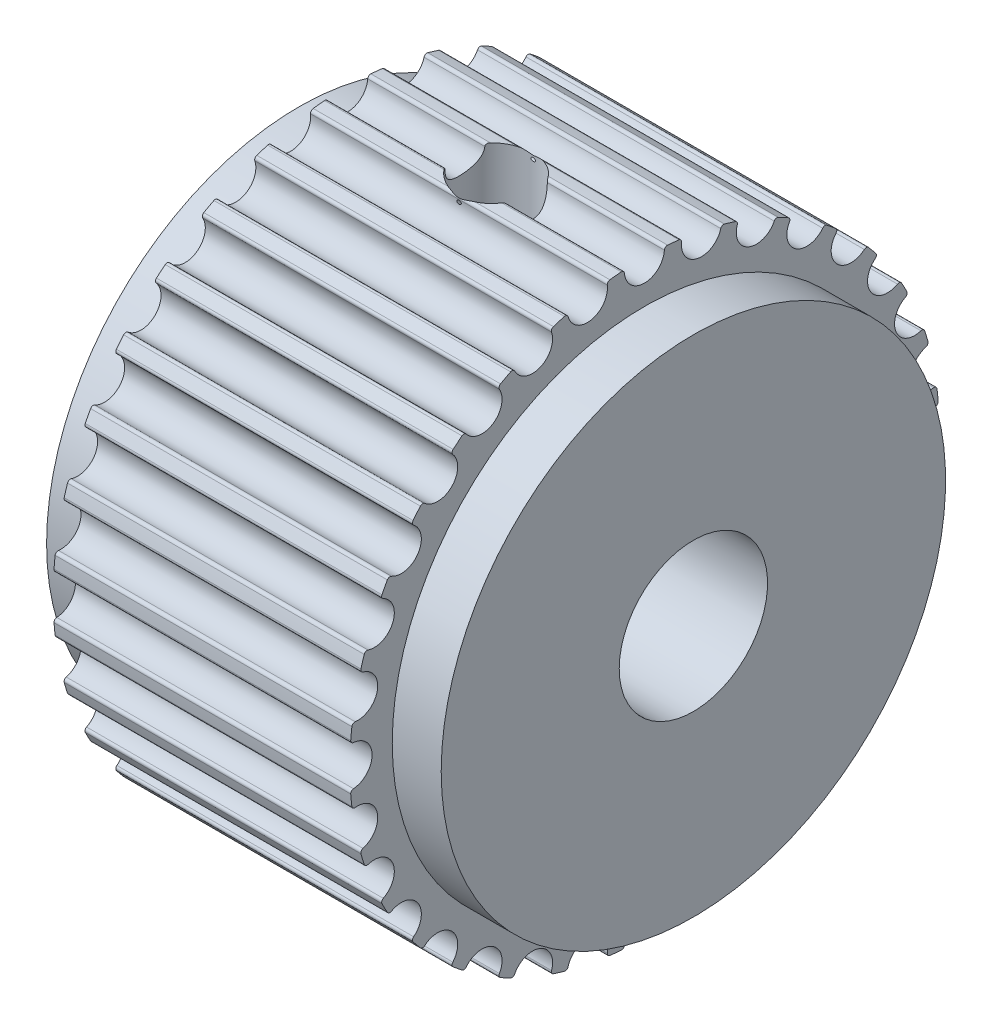
SolidWorks part; units mm, degrees
ref_plane "Front Plane" through (0, 0, 0) normal (0, 0, 1) x (1, 0, 0)
ref_plane "Top Plane" through (0, 0, 0) normal (0, 1, 0) x (1, 0, 0)
ref_plane "Right Plane" through (0, 0, 0) normal (1, 0, 0) x (0, 0, -1)
sketch "Sketch1" plane through (0, 0, 0) normal (0, 0, 1) x (1, 0, 0)
  line L0 (1.65, 10.185) -> (11.65, 10.185) construction
  line L1 (1.65, 9.93) -> (11.65, 9.93)
  line L2 (0, 8.5) -> (0, 2.5)
  line L4 (13.3, 8.5) -> (13.3, 2.5)
  line L5 (0, 2.5) -> (13.3, 2.5)
  line L6 (0, 0) -> (13.3, 0) construction
  line L8 (1.65, 8.5) -> (0, 8.5)
  line L9 (11.65, 8.5) -> (11.65, 9.93)
  line L10 (13.3, 8.5) -> (11.65, 8.5)
  line L13 (1.65, 8.5) -> (1.65, 9.93)
  dimension "D2" = 1.65
  dimension "D1" = 1.65
  dimension "O.D." = 19.86
  dimension "W" = 13.3
  dimension "E" = 17
  dimension "P.D." = 20.37
  dimension "A" = 10
  dimension "P" = 5
revolve "Revolve1" add sketch "Sketch1" angle 360 about L6
sketch "Sketch2" plane through (1.65, 0, 0) normal (1, 0, 0) x (0, 0, -1)
  line L0 (0, 0) -> (0, 9.93) construction
  circle A0 centre (0, 0) radius 9.93 construction
  circle A1 centre (0, 0) radius 9.93 construction
  arc A2 (0.673, 9.9072) -> (-0.673, 9.9072) centre (0, 0) ccw
  arc A3 (-0.673, 9.9072) -> (0.673, 9.9072) centre (0, 9.855) ccw
  circle A6 centre (0, 0) radius 9.18 construction
  circle A7 centre (0, 0) radius 10.184 construction
  dimension "MSM_3" = 0.675
  dimension "MSM_2" = 0.254
  dimension "MSM_1" = 0.75
extrude "Cut-Extrude1" cut sketch "Sketch2" along normal through all
fillet "Fillet1" radius 0.1 2 edges at (6.65, 9.9072, -0.673) (6.65, 9.9072, 0.673)
pattern_circular "CirPattern1" count 32 over 360 about axis through (0, 0, 0) along (1, 0, 0) of "Cut-Extrude1", "Fillet1"
ref_plane "Plane1" through (0, 9.93, 0) normal (0, 1, 0) x (1, 0, 0)
hole_wizard "Tapped Hole1" positions "Sketch4" profile "Sketch3" tap size "M3x0.5" standard "JIS"
sketch "Sketch4" plane through (-11.0915, 9.93, -15.1051) normal (0, 1, 0) x (1, 0, 0)
  line L0 (11.0915, -6.6051) -> (11.0915, -23.6051) construction
  line L1 (17.7415, -15.1051) -> (11.0915, -15.1051) construction
  point P0 (17.7415, -15.1051)
  dimension "D1" = 6.65
sketch "Sketch3" plane through (6.65, 9.93, 0) normal (1, 0, 0) x (0, 0, 1)
  line L0 (0, 0) -> (0, 7.43)
  line L1 (0, 7.43) -> (1.25, 7.43)
  line L2 (1.25, 7.43) -> (1.25, 0)
  line L5 (1.25, 0) -> (0, 0)
  line L11 (0, 0) -> (0, 7.43) construction
  dimension "Thru Tap Drill Dia." = 2.5
  dimension "Thru Tap Drill Depth" = 7.43
cosmetic thread "Hole Thread9" parameters "M"=3
pattern_circular "CirPattern2" count 2 every 120 about axis through (0, 0, 0) along (-1, 0, 0) of "Tapped Hole1"
hole_wizard "Tapped Hole2" [suppressed] positions "Sketch9" profile "Sketch8" tap size "M3x0.5" standard "JIS"
sketch "Sketch9" [suppressed] plane through (10.3, 8.8848, 0.534) normal (1, 0, 0) x (0, 0, -1)
  line L2 (0.534, -8.8848) -> (0.534, -16.8848) construction
  line L3 (0.534, -8.8848) -> (-6.3942, -4.8848) construction
  circle A0 centre (0.534, -8.8848) radius 8 construction
  point P0 (0.534, -16.8848)
  point P23 (-6.3942, -4.8848)
  point P24 (7.4622, -4.8848)
  dimension "QTC" = 16
  dimension "Angle_2" = 120
  dimension "Number" = 3
sketch "Sketch8" [suppressed] plane through (10.3, -8, 0) normal (0, 1, 0) x (0, 0, -1)
  line L0 (0, 0) -> (0, 9.2511)
  line L1 (0, 9.2511) -> (1.25, 8.5)
  line L2 (1.25, 8.5) -> (1.25, 0)
  line L5 (1.25, 0) -> (0, 0)
  line L10 (0, 9.2511) -> (-1.25, 8.5) construction
  line L11 (0, 0) -> (0, 9.2511) construction
  dimension "Tap Drill Dia." = 2.5
  dimension "Tap Drill Depth" = 8.5
  dimension "Drill Angle" = 118
cosmetic thread "Hole Thread2" [suppressed] parameters "Mx2"=6, "M"=3
cosmetic thread "Hole Thread3" [suppressed] parameters "Mx2"=6, "M"=3
cosmetic thread "Hole Thread4" [suppressed] parameters "Mx2"=6, "M"=3
hole_wizard "Tapped Hole3" [suppressed] positions "Sketch11" profile "Sketch10" tap size "M3x0.5" standard "JIS"
sketch "Sketch11" [suppressed] plane through (10.3, 6.1168, -5.003) normal (1, 0, 0) x (0, 0, -1)
  line L3 (-5.003, -6.1168) -> (-10.6598, -11.7737) construction
  line L4 (-5.003, -6.1168) -> (-10.6598, -0.46) construction
  line L5 (-5.003, 1.8832) -> (-5.003, -14.1168) construction
  circle A0 centre (-5.003, -6.1168) radius 8 construction
  point P22 (-10.6598, -11.7737)
  point P23 (6.0104, 6.0104)
  point P27 (-10.6598, -0.46)
  point P28 (0.6539, -0.46)
  point P29 (0.6539, -11.7737)
  dimension "QFC" = 16
  dimension "Angle_2" = 90
  dimension "Angle_1" = 45
  dimension "Number" = 4
sketch "Sketch10" [suppressed] plane through (10.3, -5.6569, 5.6569) normal (0, 1, 0) x (0, 0, -1)
  line L0 (0, 0) -> (0, 9.2511)
  line L1 (0, 9.2511) -> (1.25, 8.5)
  line L2 (1.25, 8.5) -> (1.25, 0)
  line L5 (1.25, 0) -> (0, 0)
  line L10 (0, 9.2511) -> (-1.25, 8.5) construction
  line L11 (0, 0) -> (0, 9.2511) construction
  dimension "Tap Drill Dia." = 2.5
  dimension "Tap Drill Depth" = 8.5
  dimension "Drill Angle" = 118
cosmetic thread "Hole Thread5" [suppressed] parameters "Mx2"=6, "M"=3
cosmetic thread "Hole Thread6" [suppressed] parameters "Mx2"=6, "M"=3
cosmetic thread "Hole Thread7" [suppressed] parameters "Mx2"=6, "M"=3
cosmetic thread "Hole Thread8" [suppressed] parameters "Mx2"=6, "M"=3
hole_wizard "Diameter Hole1" [suppressed] positions "Sketch15" profile "Sketch14" hole size "Ø4.0" standard "JIS"
sketch "Sketch15" [suppressed] plane through (0, 0, 0) normal (1, 0, 0) x (0, 0, -1)
  line L11 (0, 0) -> (0, -8) construction
  line L12 (0, 0) -> (-6.9282, 4) construction
  circle A2 centre (0, 0) radius 8 construction
  point P16 (0, -8)
  point P80 (-6.9282, 4)
  point P81 (6.9282, 4)
  dimension "D1" = 120
  dimension "KTC" = 16
  dimension "D2" = 3
sketch "Sketch14" [suppressed] plane through (0, -8, 0) normal (0, 1, 0) x (0, 0, 1)
  line L0 (0, 0) -> (0, 10.3)
  line L1 (0, 10.3) -> (2, 10.3)
  line L2 (2, 10.3) -> (2, 0)
  line L5 (2, 0) -> (0, 0)
  line L11 (0, 0) -> (0, 10.3) construction
  dimension "K" = 4
  dimension "Thru Hole Depth" = 10.3
hole_wizard "Diameter Hole2" [suppressed] positions "Sketch17" profile "Sketch16" hole size "Ø4.0" standard "JIS"
sketch "Sketch17" [suppressed] plane through (0, 0, 0) normal (1, 0, 0) x (0, 0, -1)
  line L18 (0, 0) -> (-5.6569, -5.6569) construction
  line L19 (0, 0) -> (-5.6569, 5.6569) construction
  line L20 (0, 8) -> (0, -8) construction
  circle A2 centre (0, 0) radius 8 construction
  point P104 (-5.6569, -5.6569)
  point P120 (-6.364, 6.364)
  point P146 (-5.6569, 5.6569)
  point P147 (5.6569, 5.6569)
  point P148 (5.6569, -5.6569)
  dimension "D1" = 90
  dimension "KFC" = 16
  dimension "D2" = 45
  dimension "D3" = 4
sketch "Sketch16" [suppressed] plane through (0, -5.6569, 5.6569) normal (0, 1, 0) x (0, 0, 1)
  line L0 (0, 0) -> (0, 10.3)
  line L1 (0, 10.3) -> (2, 10.3)
  line L2 (2, 10.3) -> (2, 0)
  line L5 (2, 0) -> (0, 0)
  line L11 (0, 0) -> (0, 10.3) construction
  dimension "K" = 4
  dimension "Thru Hole Depth" = 10.3
hole_wizard "CBORE for Socket Head Cap Screw1" [suppressed] positions "Sketch21" profile "Sketch20" counterbore size "M3" standard "JIS"
sketch "Sketch21" [suppressed] plane through (0, 0, 0) normal (-1, 0, 0) x (0, 0, 1)
  line L2 (0, 0) -> (0, -9.25) construction
  line L4 (0, 0) -> (8.0107, 4.625) construction
  circle A0 centre (0, 0) radius 9.25 construction
  circle A1 centre (8.0107, 4.625) radius 1.5 construction
  point P0 (0, -9.25)
  point P38 (-8.0107, 4.625)
  point P39 (8.0107, 4.625)
  dimension "ZTC" = 18.5
  dimension "D2" = 120
  dimension "D1" = 3
sketch "Sketch20" [suppressed] plane through (0, -9.25, 0) normal (0, 1, 0) x (0, 0, 1)
  line L0 (0, 0) -> (0, 10.3)
  line L1 (0, 10.3) -> (1.7, 10.3)
  line L3 (1.7, 10.3) -> (1.7, 3)
  line L4 (1.7, 3) -> (3.25, 3)
  line L5 (3.25, 3) -> (3.25, 0)
  line L7 (3.25, 0) -> (0, 0)
  line L11 (0, 0) -> (0, 10.3) construction
  dimension "D1_s" = 3.4
  dimension "Thru Hole Depth" = 10.3
  dimension "D2_s" = 6.5
  dimension "H_s" = 3
hole_wizard "CBORE for Socket Head Cap Screw2" [suppressed] positions "Sketch23" profile "Sketch22" counterbore size "M3" standard "JIS"
sketch "Sketch23" [suppressed] plane through (0, 0, 0) normal (-1, 0, 0) x (0, 0, 1)
  line L0 (0, 0) -> (0, 9.25) construction
  line L2 (6.5407, 6.5407) -> (0, 0) construction
  line L3 (0, 0) -> (6.5407, -6.5407) construction
  circle A0 centre (0, 0) radius 9.25 construction
  circle A1 centre (6.5407, 6.5407) radius 1.5 construction
  point P0 (6.5407, 6.5407)
  point P31 (6.5407, -6.5407)
  point P32 (-6.5407, -6.5407)
  point P33 (-6.5407, 6.5407)
  dimension "ZFC" = 18.5
  dimension "D2" = 45
  dimension "D3" = 90
  dimension "D1" = 4
sketch "Sketch22" [suppressed] plane through (0, 6.5407, 6.5407) normal (0, 1, 0) x (0, 0, 1)
  line L0 (0, 0) -> (0, 10.3)
  line L1 (0, 10.3) -> (1.75, 10.3)
  line L3 (1.75, 10.3) -> (1.75, 3.5)
  line L4 (1.75, 3.5) -> (3.25, 3.5)
  line L5 (3.25, 3.5) -> (3.25, 0)
  line L7 (3.25, 0) -> (0, 0)
  line L11 (0, 0) -> (0, 10.3) construction
  dimension "D1_s" = 3.5
  dimension "Thru Hole Depth" = 10.3
  dimension "D2_s" = 6.5
  dimension "H_s" = 3.5
equation "\"D1@Sketch4\" = \"W@Sketch1\" / 2"
equation "\"Plane dim\"= \"O.D.@Sketch1\" * 0.5"
equation "\"ZM\"=3.000000"
